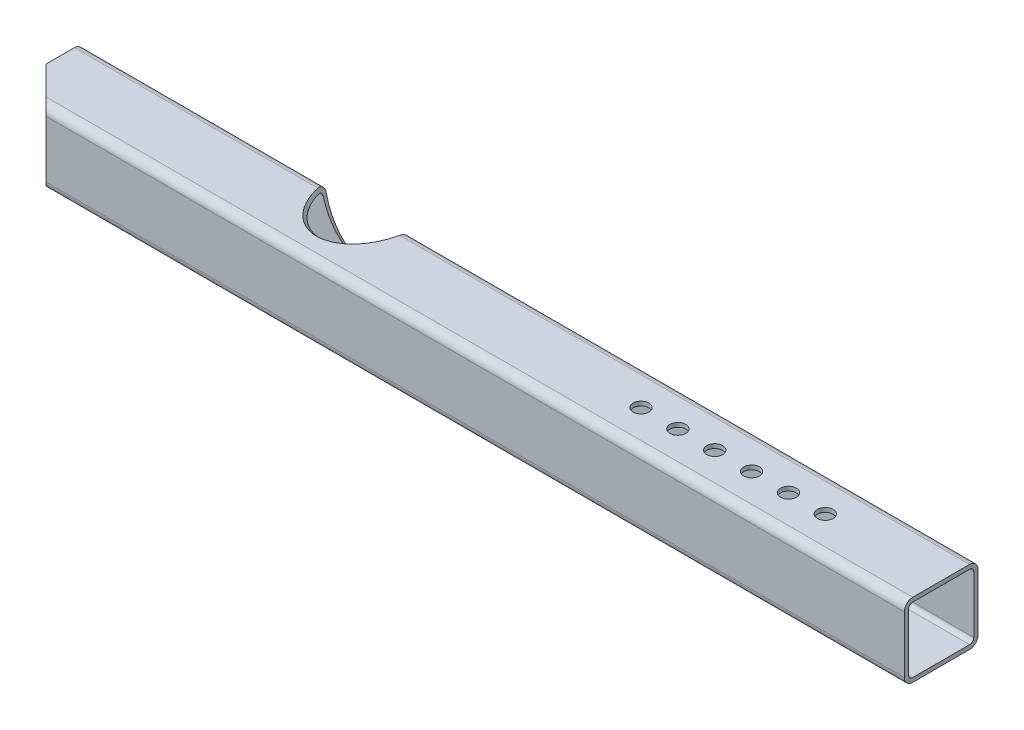
SolidWorks part; units mm, degrees
material "1.0038 (S235JRG2)"
ref_plane "Plan de face" through (0, 0, 0) normal (0, 0, 1) x (1, 0, 0)
ref_plane "Plan de dessus" through (0, 0, 0) normal (0, 1, 0) x (1, 0, 0)
ref_plane "Plan de droite" through (0, 0, 0) normal (1, 0, 0) x (0, 0, -1)
sketch "Esquisse1" plane through (0, 0, 0) normal (0, 0, 1) x (1, 0, 0)
  line L0 (-425, 0) -> (425, 0)
other "Elément mécano-soudé1"
ref_plane "Plan1" through (-425, 0, 0) normal (1, 0, 0) x (0, 1, 0)
sketch "tube carré1" plane through (-425, 0, 0) normal (1, 0, 0) x (0, 1, 0)
  line L0 (-27, 31) -> (27, 31)
  line L1 (-27, 35) -> (27, 35)
  line L2 (-35, 27) -> (-35, -27)
  line L3 (-27, -35) -> (27, -35)
  line L4 (35, 27) -> (35, -27)
  line L5 (31, 27) -> (31, -27)
  line L6 (-27, -31) -> (27, -31)
  line L7 (-31, 27) -> (-31, -27)
  line L8 (-27, 27) -> (-31, 27) construction
  line L9 (-31, 27) -> (-35, 27) construction
  line L10 (-35, 0) -> (35, 0) construction
  line L11 (0, -35) -> (0, 35) construction
  arc A0 (-27, 35) -> (-35, 27) centre (-27, 27) ccw
  arc A1 (-35, -27) -> (-27, -35) centre (-27, -27) ccw
  arc A2 (27, -35) -> (35, -27) centre (27, -27) ccw
  arc A3 (27, 35) -> (35, 27) centre (27, 27) cw
  arc A4 (27, 31) -> (31, 27) centre (27, 27) cw
  arc A5 (27, -31) -> (31, -27) centre (27, -27) ccw
  arc A6 (-31, -27) -> (-27, -31) centre (-27, -27) ccw
  arc A7 (-27, 31) -> (-31, 27) centre (-27, 27) ccw
  point P22 (-35, -35)
  point P24 (35, -35)
  point P25 (35, 35)
  point P26 (-35, 35)
  point P29 (0, 0)
  dimension "C" = 70
  dimension "e" = 4
sketch "Esquisse3" plane through (0, 35, 0) normal (0, 1, 0) x (1, 0, 0)
  line L0 (425, 27) -> (425, -27) construction
  circle A0 centre (315, 0) radius 7.5
  circle A6 centre (280, 0) radius 7.5
  circle A7 centre (245, 0) radius 7.5
  circle A8 centre (210, 0) radius 7.5
  circle A9 centre (175, 0) radius 7.5
  circle A10 centre (140, 0) radius 7.5
  dimension "D1" = 110
  dimension "D2" = 15
  dimension "D3" = 6
extrude "Enlèv. mat.-Extru.2" cut sketch "Esquisse3" against normal blind 90
sketch "Esquisse5" plane through (0, 35, 0) normal (0, 1, 0) x (1, 0, 0)
  line L0 (-425, 0) -> (-390, -35)
  line L3 (-425, 27) -> (-425, -27) construction
  line L5 (425, -35) -> (-425, -35) construction
  line L6 (-390, -35) -> (-425, -35)
  line L7 (-425, -35) -> (-425, 0)
extrude "Enlèv. mat.-Extru.3" cut sketch "Esquisse5" against normal through all
ref_plane "Plan2" through (0, 2, -2) normal (0, -0.7071, 0.7071) x (1, 0, 0)
sketch "Esquisse6" plane through (0, 2, -2) normal (0, -0.7071, 0.7071) x (1, 0, 0)
  line L1 (425, -41.0122) -> (425, -2.8284) construction
  line L2 (-425, -46.1838) -> (425, -46.1838) construction
  circle A0 centre (-155, -56.1838) radius 40.75
  point P2 (425, -21.9203)
  dimension "D1" = 81.5
  dimension "D2" = 580
  dimension "D3" = 10
extrude "Enlèv. mat.-Extru.4" [suppressed] cut sketch "Esquisse6" against normal mid plane 180
ref_plane "Plan3" through (0, 0, 0) normal (0, 0.7071, 0.7071) x (1, 0, 0)
sketch "Esquisse7" plane through (0, 0, 0) normal (0, 0.7071, 0.7071) x (1, 0, 0)
  line L0 (425, 43.8406) -> (425, 5.6569) construction
  line L1 (425, 46.1838) -> (-425, 46.1838) construction
  circle A0 centre (-155, 56.1838) radius 40.75
  dimension "D1" = 81.5
  dimension "D2" = 580
  dimension "D3" = 10
extrude "Enlèv. mat.-Extru.5" cut sketch "Esquisse7" against normal mid plane 150
